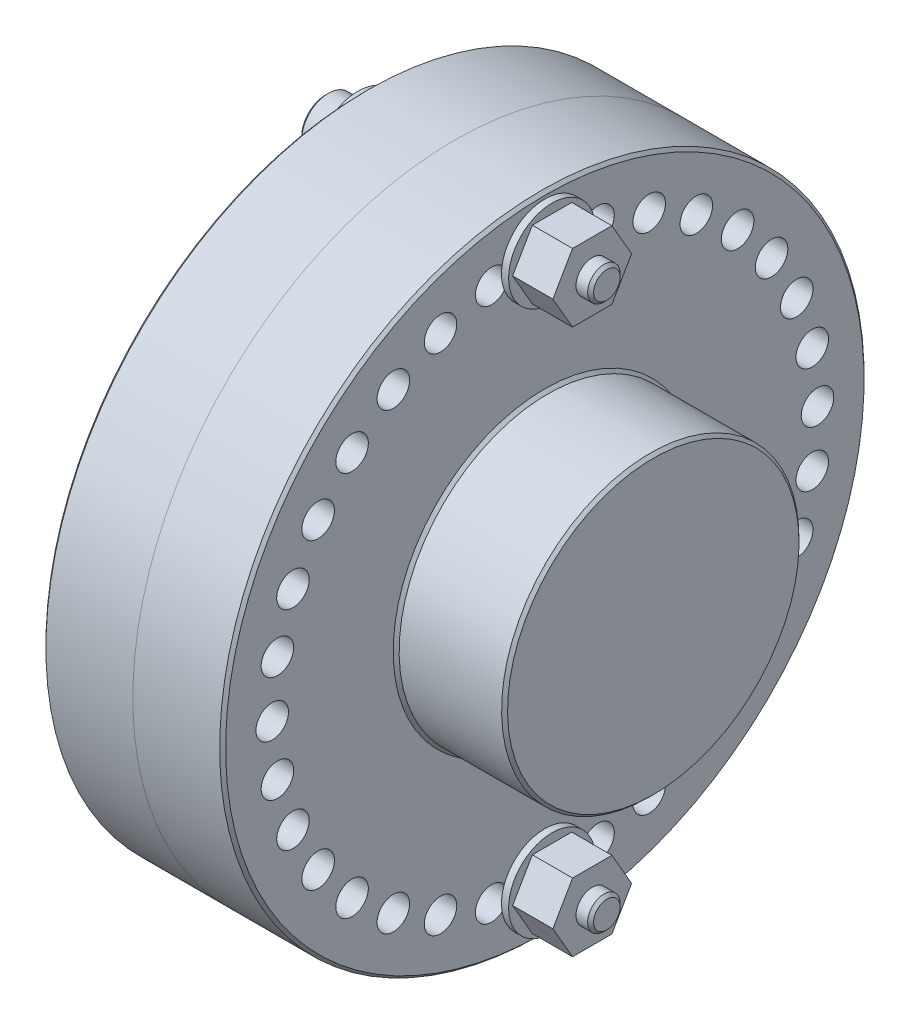
SolidWorks part; units mm, degrees
ref_plane "Front Plane" through (0, 0, 0) normal (0, 0, 1) x (1, 0, 0)
ref_plane "Top Plane" through (0, 0, 0) normal (0, 1, 0) x (1, 0, 0)
ref_plane "Right Plane" through (0, 0, 0) normal (1, 0, 0) x (0, 0, -1)
sketch "Sketch1" plane through (0, 0, 0) normal (0, 0, 1) x (1, 0, 0)
  line L0 (0, 0) -> (-25.4, 0) construction
  line L1 (0, 0) -> (0, 41.275)
  line L2 (0, 41.275) -> (-11.5094, 41.275)
  line L3 (-11.5094, 41.275) -> (-11.5094, 19.05)
  line L4 (-11.5094, 19.05) -> (-25.4, 19.05)
  line L5 (-25.4, 19.05) -> (-25.4, 0)
  line L6 (-25.4, 0) -> (0, 0)
  line L7 (0, 0) -> (-58.9413, 0) construction
  dimension "Dim K" = 25.4
  dimension "Dim A" = 82.55
  dimension "Dim E" = 11.5094
  dimension "Dim C" = 38.1
revolve "Revolve1" add sketch "Sketch1" angle 360 about L7
chamfer "Chamfer2" distance 0.381 angle 45 3 edges at (-25.4, 19.05, 0) (-11.5094, 41.275, 0) (-11.5094, 19.05, 0)
mirror "Mirror1" about plane through (0, 0, 0) normal (1, 0, 0) of bodies 101
sketch "Sketch2" plane through (-11.5094, 0, 0) normal (-1, 0, 0) x (0, 0, 1)
  line L0 (0, 34.925) -> (0, 0) construction
  circle A0 centre (0, 34.925) radius 2.0828
  circle A1 centre (0, 0) radius 34.925 construction
  circle A2 centre (6.4175, 34.3303) radius 2.0828
  circle A3 centre (12.6164, 32.5666) radius 2.0828
  circle A4 centre (18.3856, 29.6938) radius 2.0828
  circle A5 centre (23.5288, 25.8099) radius 2.0828
  circle A6 centre (27.8708, 21.047) radius 2.0828
  circle A7 centre (31.2636, 15.5674) radius 2.0828
  circle A8 centre (33.5918, 9.5577) radius 2.0828
  circle A9 centre (34.776, 3.2225) radius 2.0828
  circle A10 centre (34.776, -3.2225) radius 2.0828
  circle A11 centre (33.5918, -9.5577) radius 2.0828
  circle A12 centre (31.2636, -15.5674) radius 2.0828
  circle A13 centre (27.8708, -21.047) radius 2.0828
  circle A14 centre (23.5288, -25.8099) radius 2.0828
  circle A15 centre (18.3856, -29.6938) radius 2.0828
  circle A16 centre (12.6164, -32.5666) radius 2.0828
  circle A17 centre (6.4175, -34.3303) radius 2.0828
  circle A18 centre (0, -34.925) radius 2.0828
  circle A19 centre (-6.4175, -34.3303) radius 2.0828
  circle A20 centre (-12.6164, -32.5666) radius 2.0828
  circle A21 centre (-18.3856, -29.6938) radius 2.0828
  circle A22 centre (-23.5288, -25.8099) radius 2.0828
  circle A23 centre (-27.8708, -21.047) radius 2.0828
  circle A24 centre (-31.2636, -15.5674) radius 2.0828
  circle A25 centre (-33.5918, -9.5577) radius 2.0828
  circle A26 centre (-34.776, -3.2225) radius 2.0828
  circle A27 centre (-34.776, 3.2225) radius 2.0828
  circle A28 centre (-33.5918, 9.5577) radius 2.0828
  circle A29 centre (-31.2636, 15.5674) radius 2.0828
  circle A30 centre (-27.8708, 21.047) radius 2.0828
  circle A31 centre (-23.5288, 25.8099) radius 2.0828
  circle A32 centre (-18.3856, 29.6938) radius 2.0828
  circle A33 centre (-12.6164, 32.5666) radius 2.0828
  circle A34 centre (-6.4175, 34.3303) radius 2.0828
  dimension "D1" = 34
  dimension "Dim H" = 69.85
  dimension "Dim D" = 4.1656
extrude "Cut-Extrude1" cut sketch "Sketch2" against normal through all
sketch "Sketch3" plane through (11.5094, 0, 0) normal (1, 0, 0) x (0, 0, -1)
  circle A0 centre (0, 34.925) radius 2.0828 construction
  circle A1 centre (0, 34.925) radius 2.0828
  circle A2 centre (6.8135, 34.2539) radius 2.0828
  circle A3 centre (13.3652, 32.2665) radius 2.0828
  circle A4 centre (19.4033, 29.0391) radius 2.0828
  circle A5 centre (24.6957, 24.6957) radius 2.0828
  circle A6 centre (29.0391, 19.4033) radius 2.0828
  circle A7 centre (32.2665, 13.3652) radius 2.0828
  circle A8 centre (34.2539, 6.8135) radius 2.0828
  circle A9 centre (34.925, 0) radius 2.0828
  circle A10 centre (34.2539, -6.8135) radius 2.0828
  circle A11 centre (32.2665, -13.3652) radius 2.0828
  circle A12 centre (29.0391, -19.4033) radius 2.0828
  circle A13 centre (24.6957, -24.6957) radius 2.0828
  circle A14 centre (19.4033, -29.0391) radius 2.0828
  circle A15 centre (13.3652, -32.2665) radius 2.0828
  circle A16 centre (6.8135, -34.2539) radius 2.0828
  circle A17 centre (0, -34.925) radius 2.0828
  circle A18 centre (-6.8135, -34.2539) radius 2.0828
  circle A19 centre (-13.3652, -32.2665) radius 2.0828
  circle A20 centre (-19.4033, -29.0391) radius 2.0828
  circle A21 centre (-24.6957, -24.6957) radius 2.0828
  circle A22 centre (-29.0391, -19.4033) radius 2.0828
  circle A23 centre (-32.2665, -13.3652) radius 2.0828
  circle A24 centre (-34.2539, -6.8135) radius 2.0828
  circle A25 centre (-34.925, 0) radius 2.0828
  circle A26 centre (-34.2539, 6.8135) radius 2.0828
  circle A27 centre (-32.2665, 13.3652) radius 2.0828
  circle A28 centre (-29.0391, 19.4033) radius 2.0828
  circle A29 centre (-24.6957, 24.6957) radius 2.0828
  circle A30 centre (-19.4033, 29.0391) radius 2.0828
  circle A31 centre (-13.3652, 32.2665) radius 2.0828
  circle A32 centre (-6.8135, 34.2539) radius 2.0828
  circle A33 centre (0, -34.925) radius 2.0828 construction
  dimension "D1" = 32
extrude "Cut-Extrude2" cut sketch "Sketch3" against normal through all
sketch "Sketch4" plane through (-11.5094, 0, 0) normal (-1, 0, 0) x (0, 0, 1)
  circle A0 centre (0, 34.925) radius 2.3812
  circle A1 centre (0, 34.925) radius 5.5563
  dimension "Dim Washer OD" = 11.1125
  dimension "Dim Washer ID" = 4.7625
extrude "Boss-Extrude1" add sketch "Sketch4" along normal blind 0.9144 separate body
mirror "Mirror2" about plane through (0, 0, 0) normal (1, 0, 0) of bodies 106
ref_plane "Plane1" through (19.4564, 0, 0) normal (1, 0, 0) x (0, 0, -1)
sketch "Sketch5" plane through (-12.4238, 0, 0) normal (-1, 0, 0) x (0, 0, 1)
  circle A0 centre (0, 34.925) radius 3.429
  dimension "Dim head dia" = 6.858
extrude "Boss-Extrude2" add sketch "Sketch5" along normal blind 4.1656 separate body
sketch "Sketch6" plane through (-16.5894, 0, 0) normal (-1, 0, 0) x (0, 0, 1)
  line L1 (0, 32.8628) -> (1.7859, 33.8939)
  line L2 (1.7859, 33.8939) -> (1.7859, 35.9561)
  line L3 (1.7859, 35.9561) -> (0, 36.9872)
  line L4 (0, 36.9872) -> (-1.7859, 35.9561)
  line L5 (-1.7859, 35.9561) -> (-1.7859, 33.8939)
  line L6 (-1.7859, 33.8939) -> (0, 32.8628)
  circle A0 centre (0, 34.925) radius 1.7859 construction
  dimension "Dim socket hex width" = 3.5719
extrude "Cut-Extrude3" cut sketch "Sketch6" against normal blind 3.5719
sketch "Sketch7" plane through (-12.4238, 0, 0) normal (1, 0, 0) x (0, 0, -1)
  circle A1 centre (0, 34.925) radius 2.0828 construction
  circle A2 centre (0, 34.925) radius 2.0828
extrude "Boss-Extrude4" add sketch "Sketch7" along normal up to surface (31.8802 mm away) up to plane "Plane1"
sketch "Sketch8" plane through (12.4238, 0, 0) normal (1, 0, 0) x (0, 0, -1)
  line L1 (2.5205, 39.2906) -> (-2.5205, 39.2906)
  line L2 (-2.5205, 39.2906) -> (-5.041, 34.925)
  line L3 (-5.041, 34.925) -> (-2.5205, 30.5594)
  line L4 (-2.5205, 30.5594) -> (2.5205, 30.5594)
  line L5 (2.5205, 30.5594) -> (5.041, 34.925)
  line L6 (5.041, 34.925) -> (2.5205, 39.2906)
  circle A0 centre (0, 34.925) radius 2.0828
  circle A1 centre (0, 34.925) radius 2.0828 construction
  circle A2 centre (0, 34.925) radius 4.3656 construction
  dimension "Dim nut width" = 8.7312
extrude "Boss-Extrude5" add sketch "Sketch8" along normal blind 5.1562 separate body
chamfer "Chamfer1" distance 0.381 angle 45 2 edges at (19.4564, 37.0078, 0) (-16.5894, 31.496, 0)
mirror "Mirror3" about plane through (0, 0, 0) normal (0, 1, 0) of bodies 112 111 107 106
